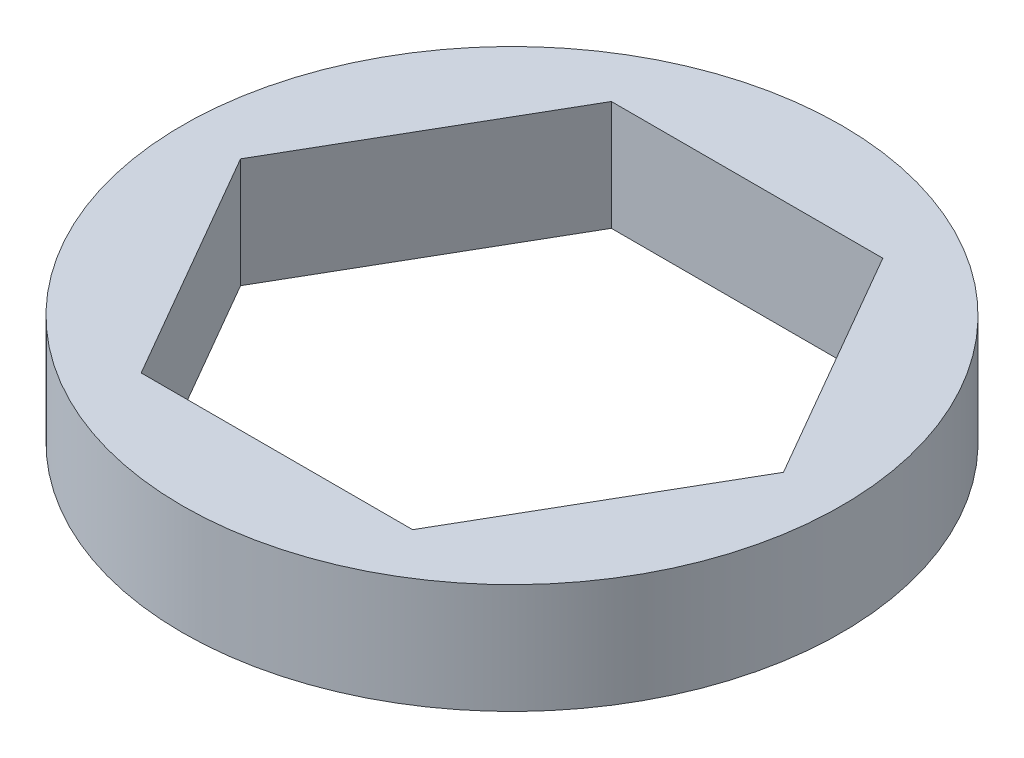
SolidWorks part; units mm, degrees
ref_plane "Front" through (0, 0, 0) normal (0, 0, 1) x (1, 0, 0)
ref_plane "Top" through (0, 0, 0) normal (0, 1, 0) x (1, 0, 0)
ref_plane "Right" through (0, 0, 0) normal (1, 0, 0) x (0, 0, -1)
sketch "Sketch1" plane through (0, 0, 0) normal (0, 1, 0) x (1, 0, 0)
  line L1 (3.9228, -6.7945) -> (7.8456, 0)
  line L2 (7.8456, 0) -> (3.9228, 6.7945)
  line L3 (3.9228, 6.7945) -> (-3.9228, 6.7945)
  line L4 (-3.9228, 6.7945) -> (-7.8456, 0)
  line L5 (-7.8456, 0) -> (-3.9228, -6.7945)
  line L6 (-3.9228, -6.7945) -> (3.9228, -6.7945)
  circle A0 centre (0, 0) radius 6.7945 construction
  circle A1 centre (0, 0) radius 9.525
  dimension "D1" = 19.05
extrude "Boss-Extrude1" add sketch "Sketch1" along normal blind 3.175
